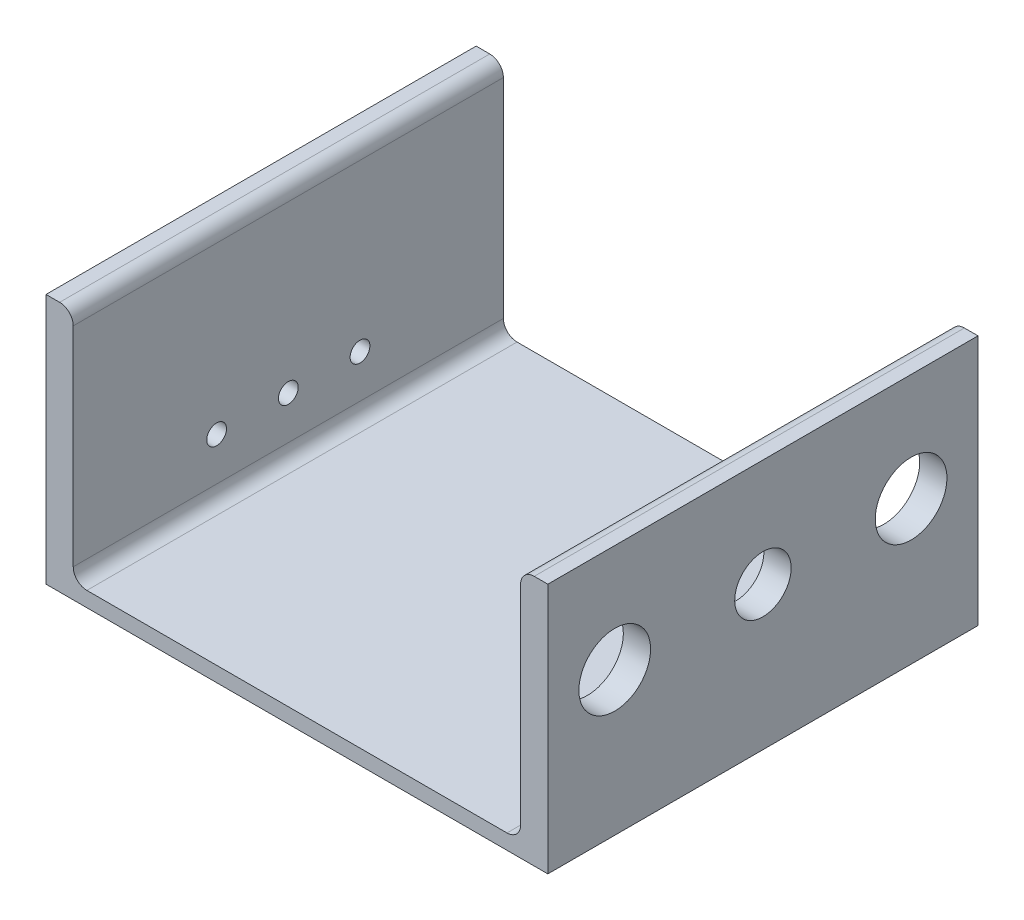
SolidWorks part; units mm, degrees
ref_plane "Front" through (0, 0, 0) normal (0, 0, 1) x (1, 0, 0)
ref_plane "Top" through (0, 0, 0) normal (0, 1, 0) x (1, 0, 0)
ref_plane "Right" through (0, 0, 0) normal (1, 0, 0) x (0, 0, -1)
sketch "Sketch1" plane through (0, 0, 0) normal (0, 0, 1) x (1, 0, 0)
  line L0 (-79.248, 88.9) -> (-88.9, 88.9)
  line L1 (-88.9, 88.9) -> (-88.9, 0)
  line L2 (-88.9, 0) -> (88.9, 0)
  line L3 (88.9, 0) -> (88.9, 88.9)
  line L4 (88.9, 88.9) -> (79.248, 88.9)
  line L5 (79.248, 88.9) -> (79.248, 5.334)
  line L6 (79.248, 5.334) -> (-79.248, 5.334)
  line L7 (-79.248, 5.334) -> (-79.248, 88.9)
  dimension "Leg THickness" = 9.652
  dimension "BaseThickness" = 5.334
  dimension "LegLength" = 88.9
  dimension "BaseWidth" = 177.8
extrude "Boss-Extrude1" add sketch "Sketch1" along normal mid plane 152.4
fillet "Fillet1" radius 4.826 4 edges at (79.248, 88.9, 0) (-79.248, 88.9, 0) (-79.248, 5.334, 0) (79.248, 5.334, 0)
sketch "Sketch2" plane through (88.9, 0, 0) normal (1, 0, 0) x (0, 0, -1)
  line L0 (0, 50.8) -> (0, 90.8461) construction
  line L1 (-76.2, 0) -> (76.2, 0) construction
  circle A0 centre (52.5, 50.8) radius 12.7
  circle A1 centre (-52.5, 50.8) radius 12.7
  circle A2 centre (0, 50.8) radius 10
  point P7 (0, 16.8716)
  dimension "D1" = 25.4
  dimension "D3" = 20
  dimension "D2" = 52.5
  dimension "D4" = 50.8
extrude "Cut-Extrude1" cut sketch "Sketch2" against normal up to surface (9.652 mm away) up to face at (79.248, 47.117, 0)
sketch "Sketch3" plane through (-88.9, 0, 0) normal (-1, 0, 0) x (0, 0, 1)
  line L0 (0, 0) -> (0, 88.9) construction
  line L1 (76.2, 0) -> (-76.2, 0) construction
  line L2 (76.2, 88.9) -> (-76.2, 88.9) construction
  circle A1 centre (-25.4, 25.4) radius 3.5
  circle A2 centre (25.4, 25.4) radius 3.5
  circle A4 centre (0, 25.4) radius 3.5
  dimension "D1" = 25.4
  dimension "D2" = 7
  dimension "D3" = 25.4
  dimension "D4" = 7
extrude "Cut-Extrude2" cut sketch "Sketch3" against normal up to surface (9.652 mm away) up to face at (-79.248, 47.117, 0)
equation "\"D1@Fillet1\" = \"Leg THickness@Sketch1\"/2"
